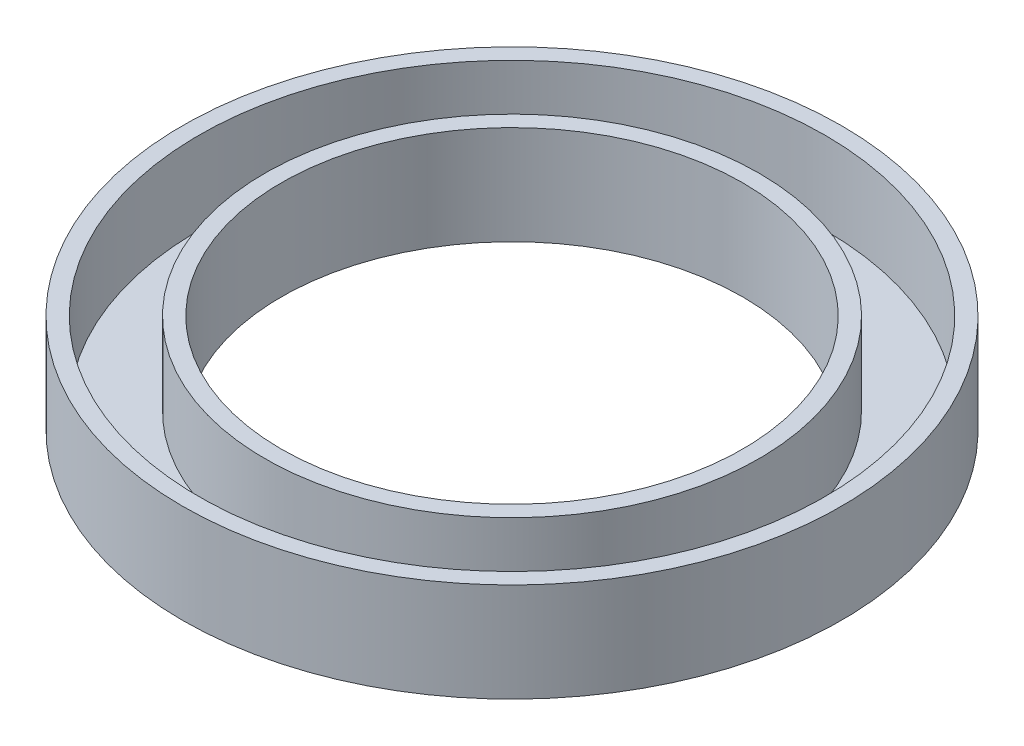
SolidWorks part; units mm, degrees
material "BUNA N"
ref_plane "Front" through (0, 0, 0) normal (0, 0, 1) x (1, 0, 0)
ref_plane "Top" through (0, 0, 0) normal (0, 1, 0) x (1, 0, 0)
ref_plane "Right" through (0, 0, 0) normal (1, 0, 0) x (0, 0, -1)
sketch "Sketch1" plane through (0, 0, 0) normal (0, 0, 1) x (1, 0, 0)
  line L0 (-15.875, 4.7625) -> (-15.875, 0)
  line L1 (-15.875, 0) -> (-11.1125, 0)
  line L2 (-11.1125, 0) -> (-11.1125, 4.7625)
  line L3 (-11.1125, 4.7625) -> (-11.9062, 4.7625)
  line L4 (-11.9062, 4.7625) -> (-11.9062, 0.7937)
  line L5 (-11.9062, 0.7937) -> (-15.0813, 0.7937)
  line L6 (-15.0813, 0.7937) -> (-15.0813, 4.7625)
  line L7 (-15.0813, 4.7625) -> (-15.875, 4.7625)
  line L8 (0, 0) -> (0, 4.7625) construction
  dimension "D1" = 15.875
  dimension "D2" = 4.7625
  dimension "D3" = 11.1125
  dimension "D4" = 0.7937
  dimension "D5" = 0.7937
revolve "Revolve1" add sketch "Sketch1" angle 360 about L8
equation "\"D5@Sketch1\"=\"D4@Sketch1\""
